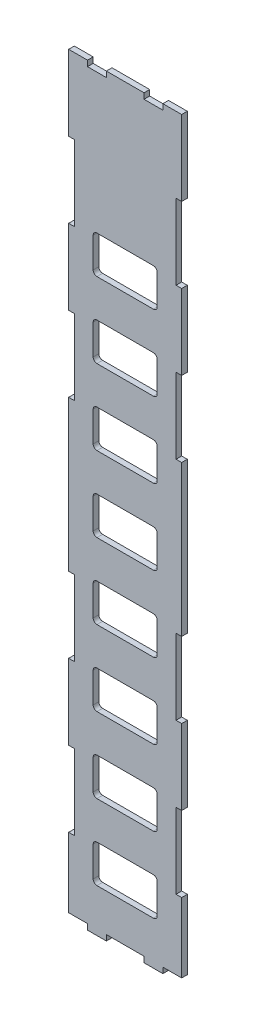
SolidWorks part; units mm, degrees
ref_plane "Front Plane" through (0, 0, 0) normal (0, 0, 1) x (1, 0, 0)
ref_plane "Top Plane" through (0, 0, 0) normal (0, 1, 0) x (1, 0, 0)
ref_plane "Right Plane" through (0, 0, 0) normal (1, 0, 0) x (0, 0, -1)
sketch "Sketch1" plane through (0, 0, 0) normal (0, 0, 1) x (1, 0, 0)
  line L1 (30, 200) -> (-30, 200)
  line L2 (30, 200) -> (30, -200)
  line L3 (30, -200) -> (-30, -200)
  line L4 (-30, 200) -> (-30, -200)
  line L5 (30, 200) -> (-30, -200) construction
  line L6 (30, -200) -> (-30, 200) construction
  point P0 (0, 0)
extrude "Boss-Extrude1" add sketch "Sketch1" along normal blind 3
sketch "Sketch2" plane through (0, 0, 3) normal (0, 0, 1) x (1, 0, 0)
  line L1 (-27, 40) -> (-30, 40)
  line L2 (-27, 80) -> (-30, 80)
  line L3 (-27, 120) -> (-30, 120)
  line L4 (-30, 200) -> (-30, -200)
  line L5 (-30, -200) -> (30, -200)
  line L6 (30, -200) -> (30, 200)
  line L7 (30, 200) -> (-30, 200)
  line L8 (-30, 160) -> (-30, 80)
  line L9 (-27, -200) -> (-20, -200)
  line L10 (-30, -120) -> (-30, -160)
  line L11 (20, 200) -> (10, 200)
  line L12 (30, 160) -> (27, 160)
  line L13 (30, 120) -> (27, 120)
  line L14 (30, 80) -> (27, 80)
  line L15 (30, 40) -> (27, 40)
  line L16 (-27, 197) -> (-27, -197)
  line L17 (-27, -197) -> (27, -197)
  line L18 (27, -197) -> (27, 197)
  line L19 (27, 197) -> (-27, 197)
  line L20 (-10, 200) -> (-20, 200)
  line L21 (-27, -197) -> (-20, -197)
  line L22 (27, -200) -> (27, -197)
  line L23 (20, 197) -> (10, 197)
  line L24 (-10, -197) -> (10, -197)
  line L25 (30, -40) -> (27, -40)
  line L26 (30, -80) -> (27, -80)
  line L27 (30, -120) -> (27, -120)
  line L28 (30, -160) -> (27, -160)
  line L29 (-27, -160) -> (-30, -160)
  line L30 (-27, -120) -> (-30, -120)
  line L31 (-27, -80) -> (-30, -80)
  line L32 (-27, -40) -> (-30, -40)
  line L33 (-27, 160) -> (-30, 160)
  line L34 (-27, 160) -> (-27, 120)
  line L35 (-10, 197) -> (-20, 197)
  line L36 (-27, -120) -> (-27, -160)
  line L37 (-27, -197) -> (-27, -200)
  line L38 (27, -160) -> (27, -120)
  line L39 (30, -160) -> (30, -120)
  line L40 (27, -80) -> (27, -40)
  line L41 (30, -80) -> (30, -40)
  line L42 (-30, 80) -> (-30, 40)
  line L43 (-27, 80) -> (-27, 40)
  line L44 (27, 120) -> (27, 160)
  line L45 (30, 120) -> (30, 160)
  line L46 (-30, -40) -> (-30, -80)
  line L47 (-27, -40) -> (-27, -80)
  line L48 (27, 40) -> (27, 80)
  line L49 (30, 40) -> (30, 80)
  line L50 (30, 0) -> (27, 0)
  line L51 (-10, -200) -> (10, -200)
  line L53 (20, -197) -> (27, -197)
  line L54 (-30, -200) -> (-27, -200)
  line L55 (-20, -197) -> (-20, -200)
  line L56 (-20, 200) -> (-20, 197)
  line L57 (-10, -197) -> (-10, -200)
  line L58 (-10, 200) -> (-10, 197)
  line L61 (10, -197) -> (10, -200)
  line L62 (10, 200) -> (10, 197)
  line L63 (20, -197) -> (20, -200)
  line L64 (20, 200) -> (20, 197)
  line L65 (20, -200) -> (27, -200)
  dimension "D1" = 0
  dimension "D2" = 3
  dimension "D3" = 10
extrude "Cut-Extrude3" cut sketch "Sketch2" against normal blind 3 contours L55 L21 L37 L2 | L61 L24 L57 L2 | L53 L63 L2 L22 | L36 L30 L1 L29 | L38 L28 L3 L27 | L47 L32 L1 L31 | L40 L26 L3 L25 | L43 L2 L1 | L48 L15 L3 L14 | L34 L33 L1 L3 | L44 L13 L3 L12 | L58 L4 L56 L35 | L64 L4 L62 L23
sketch "Sketch3" plane through (0, 0, 3) normal (0, 0, 1) x (1, 0, 0)
  line L0 (-30, -200) -> (-27, -200) construction
  line L1 (-30, -200) -> (-27, -200)
  line L2 (27, -200) -> (30, -200) construction
  line L3 (30, -200) -> (30, -160) construction
  line L4 (27, -200) -> (27, -197) construction
  line L5 (-30, -160) -> (-30, -200) construction
  line L6 (-27, -197) -> (-27, -200) construction
  line L7 (27, -200) -> (30, -200)
  line L8 (30, -200) -> (30, -197)
  line L9 (27, -200) -> (27, -197)
  line L10 (-30, -197) -> (-30, -200)
  line L11 (-27, -197) -> (-27, -200)
  line L12 (27, -197) -> (30, -197)
  line L13 (-30, -197) -> (-27, -197)
extrude "Cut-Extrude4" cut sketch "Sketch3" against normal blind 3
sketch "Sketch4" plane through (0, 0, 3) normal (0, 0, 1) x (1, 0, 0)
  line L55 (-17, -157) -> (17, -157)
  line L56 (-10, -177) -> (10, -177)
  line L57 (-17, -177) -> (17, -177)
  line L58 (-17, -137) -> (17, -137)
  line L60 (-17, -117) -> (17, -117)
  line L62 (-17, -177) -> (-17, -157)
  line L63 (17, -177) -> (17, -157)
  line L64 (-17, -97) -> (17, -97)
  line L65 (-17, -77) -> (17, -77)
  line L66 (-17, -57) -> (17, -57)
  line L67 (-17, -37) -> (17, -37)
  line L68 (-17, -17) -> (17, -17)
  line L69 (-17, 3) -> (17, 3)
  line L70 (-17, 23) -> (17, 23)
  line L71 (-17, 43) -> (17, 43)
  line L72 (-17, 63) -> (17, 63)
  line L73 (-17, 83) -> (17, 83)
  line L74 (-17, 103) -> (17, 103)
  line L75 (-17, 123) -> (17, 123)
  line L78 (-17, -137) -> (-17, -117)
  line L79 (17, -137) -> (17, -117)
  line L81 (-17, -97) -> (-17, -77)
  line L82 (17, -97) -> (17, -77)
  line L83 (-17, -57) -> (-17, -37)
  line L84 (17, -57) -> (17, -37)
  line L85 (-17, -17) -> (-17, 3)
  line L86 (17, -17) -> (17, 3)
  line L87 (-17, 23) -> (-17, 43)
  line L88 (17, 23) -> (17, 43)
  line L89 (-17, 63) -> (-17, 83)
  line L90 (17, 63) -> (17, 83)
  line L91 (-17, 103) -> (-17, 123)
  line L92 (17, 103) -> (17, 123)
  line L159 (-17, 183) -> (17, 183) [skipped]
  line L160 (-17, 143) -> (17, 143) [skipped]
  line L161 (-17, 163) -> (17, 163) [skipped]
  dimension "D1" = 20
  dimension "D2" = 19
extrude "Cut-Extrude5" cut sketch "Sketch4" against normal blind 3
fillet "Fillet1" radius 2 32 edges at (-17, 123, 1.5) (-17, 103, 1.5) (17, 123, 1.5) (17, 103, 1.5) (17, 63, 1.5) (-17, 63, 1.5) (-17, 83, 1.5) (17, 83, 1.5) (17, 43, 1.5) (17, 23, 1.5) (-17, 23, 1.5) (-17, 43, 1.5) (-17, 3, 1.5) (17, 3, 1.5) (17, -17, 1.5) (-17, -17, 1.5) (-17, -57, 1.5) (17, -57, 1.5) (17, -37, 1.5) (-17, -37, 1.5) (-17, -77, 1.5) (17, -77, 1.5) (17, -117, 1.5) (-17, -117, 1.5) (17, -97, 1.5) (17, -137, 1.5) (-17, -97, 1.5) (-17, -137, 1.5) (-17, -177, 1.5) (17, -177, 1.5) (17, -157, 1.5) (-17, -157, 1.5)
